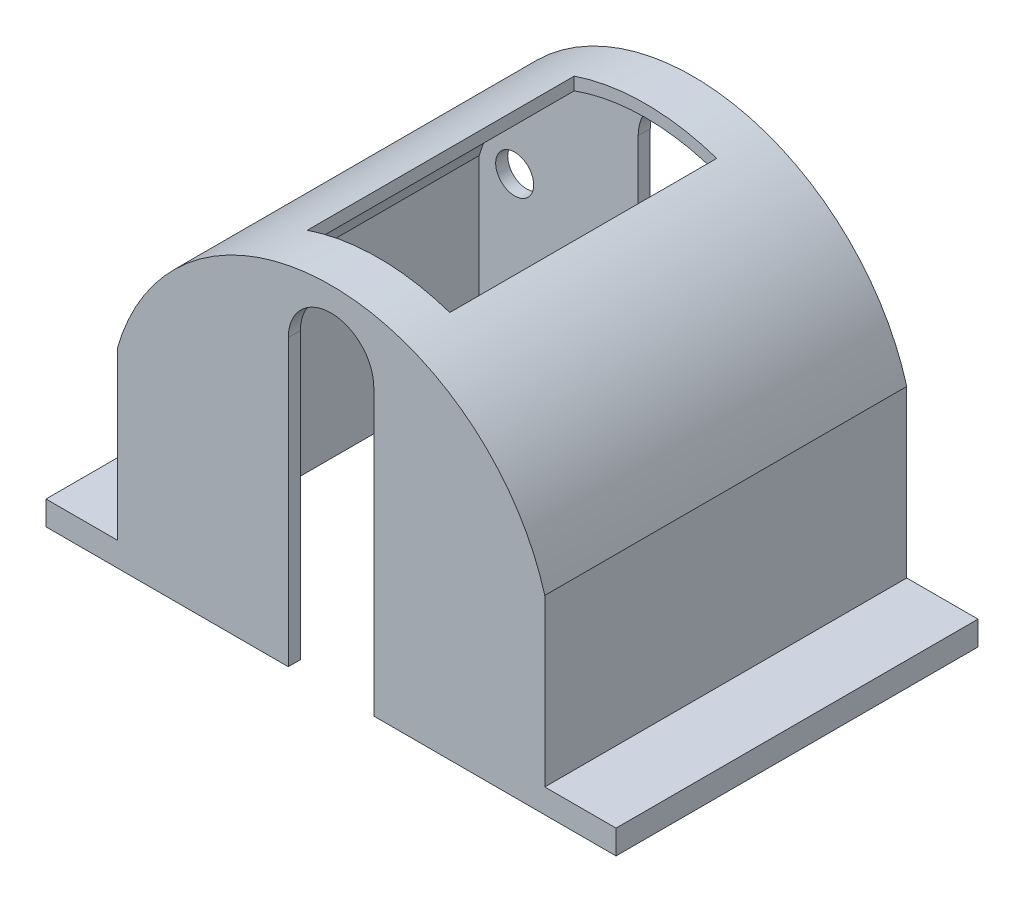
SolidWorks part; units mm, degrees
ref_plane "Front Plane" through (0, 0, 0) normal (0, 0, 1) x (1, 0, 0)
ref_plane "Top Plane" through (0, 0, 0) normal (0, 1, 0) x (1, 0, 0)
ref_plane "Right Plane" through (0, 0, 0) normal (1, 0, 0) x (0, 0, -1)
sketch "Sketch1" plane through (0, 0, 0) normal (0, 0, 1) x (1, 0, 0)
  line L0 (0, 0) -> (0, 7.5) construction
  line L1 (-17.5, 0) -> (0, 0) construction
  line L2 (-17.5, 0) -> (-17.5, 17.025) construction
  line L3 (-17.5, 17.025) -> (17.5, 17.025) construction
  line L4 (17.5, 17.025) -> (17.5, 0) construction
  line L5 (-22.5, 0) -> (22.5, 0) construction
  line L6 (-22.5, 0) -> (-22.5, -20)
  line L7 (-22.5, -20) -> (22.5, -20)
  line L8 (22.5, -20) -> (22.5, 0)
  arc A2 (-22.5, 0) -> (22.5, 0) centre (0, -6.3553) cw
  point P4 (4.1405, -20)
  point P6 (0, 0)
  point P13 (0, 0)
  point P15 (3.1582, -20)
  point P16 (0, 0)
  dimension "D1" = 45
  dimension "D2" = 35
  dimension "D3" = 9.525
  dimension "D4" = 5
  dimension "D5" = 5
  dimension "D6" = 7.5
  dimension "D8" = 20
extrude "Boss-Extrude3" add sketch "Sketch1" along normal blind 38.1 contours L6 L7 L8 A2
shell "Shell1" thickness 1.27
sketch "Sketch3" plane through (0, 0, 0) normal (0, 0, -1) x (-1, 0, 0)
  line L0 (-4.5, 10) -> (-4.5, -20)
  line L1 (4.5, 10) -> (4.5, -20)
  line L2 (22.5, -20) -> (-22.5, -20) construction
  line L3 (0, 10) -> (0, -20) construction
  line L4 (-4.5, -20) -> (4.5, -20)
  arc A2 (4.5, 10) -> (-4.5, 10) centre (0, 10) ccw
  dimension "D1" = 9
  dimension "D2" = 30
extrude "Cut-Extrude1" cut sketch "Sketch3" against normal through all contours L0 L4 L1 A2
sketch "Sketch4" plane through (0, 0, 0) normal (0, 0, -1) x (-1, 0, 0)
  line L0 (0, 0) -> (0, 17.025) construction
  line L1 (-17.5, 0) -> (-22.5, 0) construction
  arc A0 (22.5, 0) -> (-22.5, 0) centre (0, -6.3553) ccw construction
  circle A1 centre (-17.5, 0) radius 2
  circle A2 centre (17.5, 0) radius 2
  point P10 (-17.5, 0)
  dimension "D2" = 4
  dimension "D1" = 35
extrude "Cut-Extrude2" cut sketch "Sketch4" against normal blind 2.54
sketch "Sketch5" plane through (0, 0, 0) normal (0, 1, 0) x (1, 0, 0)
  line L0 (22.5, 0) -> (-22.5, 0) construction
  line L1 (-7.5, -33.1) -> (7.5, -33.1)
  line L2 (-7.5, -33.1) -> (-7.5, -5)
  line L3 (-7.5, -5) -> (7.5, -5)
  line L4 (7.5, -33.1) -> (7.5, -5)
  line L5 (-22.5, -38.1) -> (22.5, -38.1) construction
  line L7 (0, 0) -> (0, -38.1) construction
  point P10 (0, -5)
  dimension "D1" = 5
  dimension "D2" = 5
  dimension "D4" = 15
extrude "Cut-Extrude3" cut sketch "Sketch5" against normal through all both and the other way through all
sketch "Sketch6" plane through (0, -20, 0) normal (0, -1, 0) x (1, 0, 0)
  line L0 (0, 0) -> (0, 38.1) construction
  line L1 (-22.5, 38.1) -> (-30, 38.1)
  line L2 (-22.5, 38.1) -> (-22.5, 0)
  line L3 (-22.5, 0) -> (-30, 0)
  line L4 (-30, 38.1) -> (-30, 0)
  line L5 (4.5, 38.1) -> (-4.5, 38.1) construction
  line L6 (30, 38.1) -> (22.5, 38.1)
  line L7 (30, 38.1) -> (30, 0)
  line L8 (30, 0) -> (22.5, 0)
  line L9 (22.5, 38.1) -> (22.5, 0)
  line L10 (-22.5, 0) -> (-4.5, 0) construction
  point P14 (22.5, 50.8)
  point P16 (22.5, 0)
  point P18 (-22.5, 0)
  dimension "D1" = 7.5
extrude "Boss-Extrude4" add sketch "Sketch6" against normal blind 2.54
